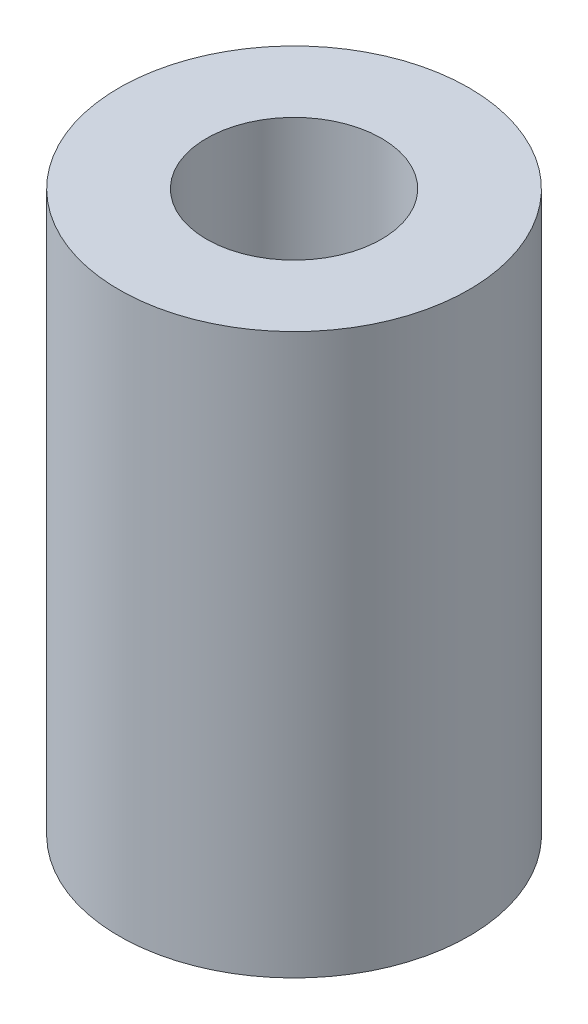
SolidWorks part; units mm, degrees
ref_plane "Front Plane" through (0, 0, 0) normal (0, 0, 1) x (1, 0, 0)
ref_plane "Top Plane" through (0, 0, 0) normal (0, 1, 0) x (1, 0, 0)
ref_plane "Right Plane" through (0, 0, 0) normal (1, 0, 0) x (0, 0, -1)
sketch "Sketch1" plane through (0, 0, 0) normal (0, 0, 1) x (1, 0, 0)
  line L0 (0, 0) -> (0, 15.7251) construction
  line L1 (2.5, 16) -> (2.5, 0)
  line L2 (2.5, 0) -> (5, 0)
  line L4 (2.5, 16) -> (5, 16)
  line L5 (5, 0) -> (5, 16)
  dimension "D2" = 16
revolve "Revolve1" add sketch "Sketch1" angle 360 about L0
